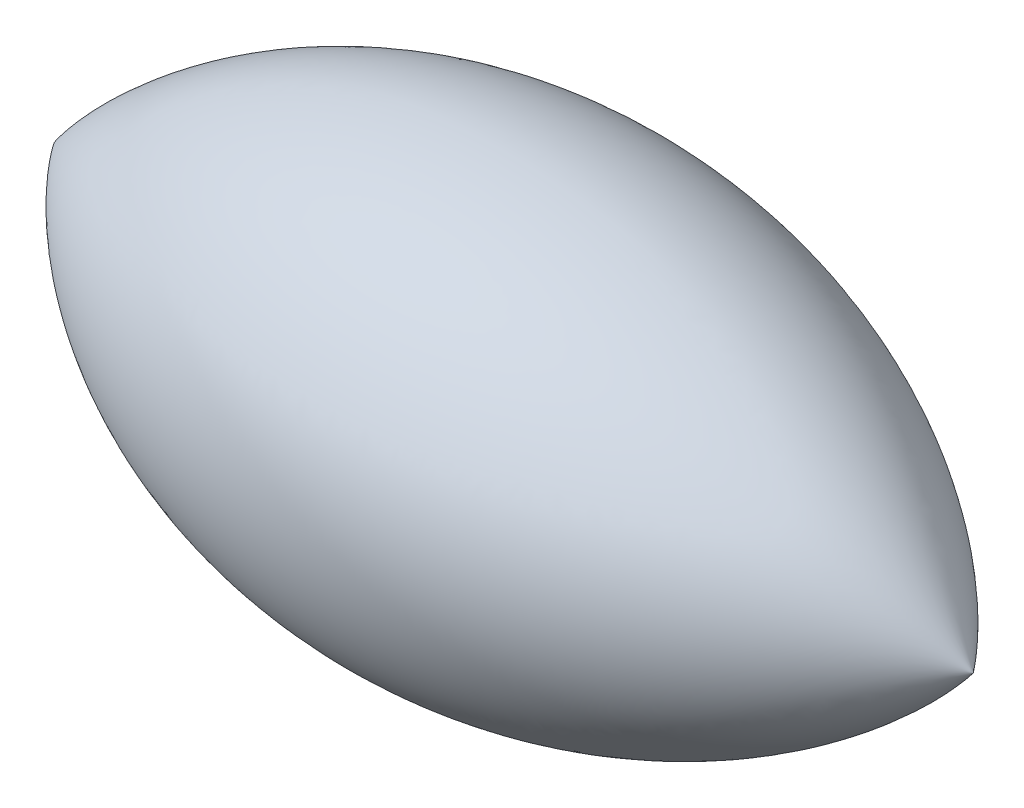
SolidWorks part; units mm, degrees
ref_plane "Front" through (0, 0, 0) normal (0, 0, 1) x (1, 0, 0)
ref_plane "Top" through (0, 0, 0) normal (0, 1, 0) x (1, 0, 0)
ref_plane "Right" through (0, 0, 0) normal (1, 0, 0) x (0, 0, -1)
sketch "Sketch1" plane through (0, 0, 0) normal (0, 0, 1) x (1, 0, 0)
  line L0 (-419.6577, 142.961) -> (451.481, 142.961) construction
  line L1 (-419.6577, 142.961) -> (451.481, 142.961)
  spline S0 degree 3 poles (-419.6577, 142.961) (-209.0103, 427.7177) (237.0576, 411.0391) (451.481, 142.961) knots 0 0 0 0 1 1 1 1
  point P2 (451.481, 143.428)
  point P4 (-419.6577, 142.961)
revolve "Revolve1" add sketch "Sketch1" angle 360 about L0
